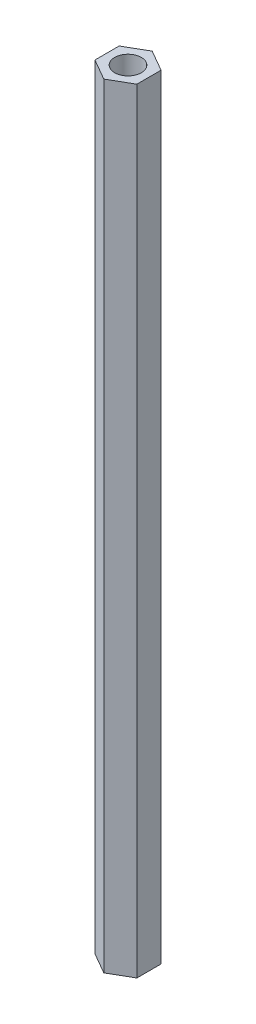
SolidWorks part; units mm, degrees
ref_plane "Front Plane" through (0, 0, 0) normal (0, 0, 1) x (1, 0, 0)
ref_plane "Top Plane" through (0, 0, 0) normal (0, 1, 0) x (1, 0, 0)
ref_plane "Right Plane" through (0, 0, 0) normal (1, 0, 0) x (0, 0, -1)
sketch "Sketch1" plane through (0, 0, 0) normal (0, 1, 0) x (1, 0, 0)
  line L1 (2.75, -1.5877) -> (2.75, 1.5877)
  line L2 (2.75, 1.5877) -> (0, 3.1754)
  line L3 (0, 3.1754) -> (-2.75, 1.5877)
  line L4 (-2.75, 1.5877) -> (-2.75, -1.5877)
  line L5 (-2.75, -1.5877) -> (0, -3.1754)
  line L6 (0, -3.1754) -> (2.75, -1.5877)
  circle A0 centre (0, 0) radius 2.75 construction
  circle A1 centre (0, 0) radius 1.75
  dimension "D2" = 3.5
  dimension "D1" = 5.5
extrude "Boss-Extrude1" add sketch "Sketch1" along normal blind 101.6
